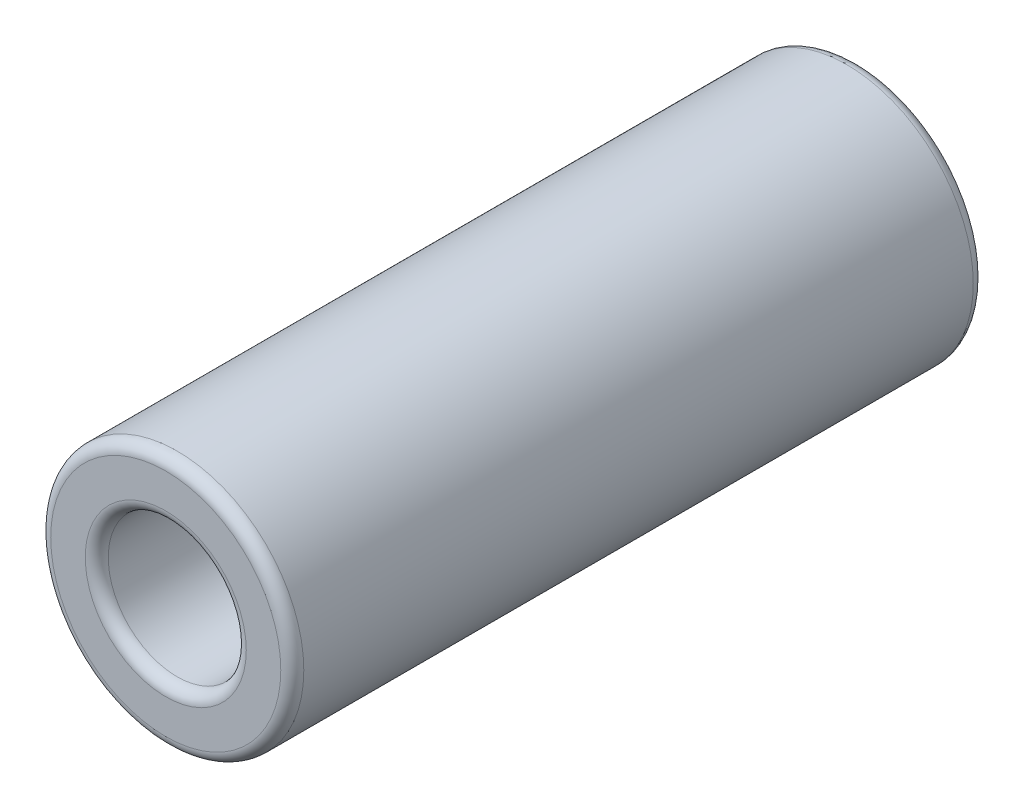
SolidWorks part; units mm, degrees
material "Cast Alloy Steel"
ref_plane "Front Plane" through (0, 0, 0) normal (0, 0, 1) x (1, 0, 0)
ref_plane "Top Plane" through (0, 0, 0) normal (0, 1, 0) x (1, 0, 0)
ref_plane "Right Plane" through (0, 0, 0) normal (1, 0, 0) x (0, 0, -1)
sketch "Sketch1" plane through (0, 0, 0) normal (0, 0, 1) x (1, 0, 0)
  circle A0 centre (0, 0) radius 5.5
  dimension "D1" = 11
extrude "Boss-Extrude1" add sketch "Sketch1" along normal blind 30.1
sketch "Sketch2" plane through (0, 0, 30.1) normal (0, 0, 1) x (1, 0, 0)
  circle A0 centre (0, 0) radius 3
extrude "Cut-Extrude1" cut sketch "Sketch2" against normal through all
fillet "Fillet1" radius 0.5 4 edges at (5.5, 0, 0) (3, 0, 0) (5.5, 0, 30.1) (3, 0, 30.1)
